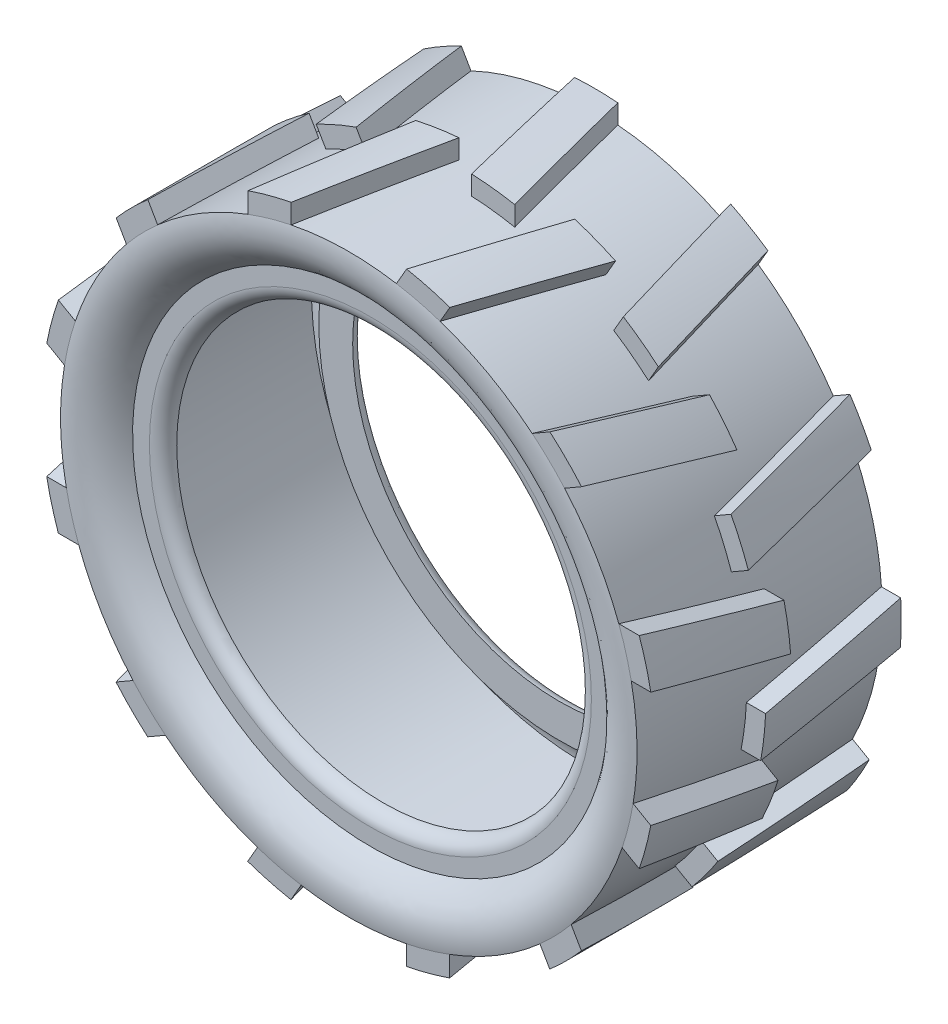
SolidWorks part; units mm, degrees
material "ABS"
ref_plane "Спереди" through (0, 0, 0) normal (0, 0, 1) x (1, 0, 0)
ref_plane "Сверху" through (0, 0, 0) normal (0, 1, 0) x (1, 0, 0)
ref_plane "Справа" through (0, 0, 0) normal (1, 0, 0) x (0, 0, -1)
sketch "Эскиз1" plane through (0, 0, 0) normal (1, 0, 0) x (0, 0, -1)
  line L0 (-131.0476, 0) -> (127.548, 0) construction
  line L1 (0, 0) -> (0, 104.7617) construction
  line L2 (0, 60) -> (25.5, 60)
  line L3 (21, 49.5) -> (21, 46)
  line L5 (18.3095, 50.0522) -> (18.3095, 46)
  line L14 (18.3095, 46) -> (18.3095, 43)
  line L16 (25.5, 60) -> (21, 49.5) construction
  line L17 (0, 57.3095) -> (21.4198, 57.3095) construction
  line L18 (21.4198, 57.3095) -> (18.3095, 50.0522) construction
  line L20 (19.831, 51.1228) -> (18.3095, 50.0522)
  line L21 (-19.831, 51.1228) -> (-18.3095, 50.0522)
  line L23 (-18.3095, 46) -> (-18.3095, 43)
  line L24 (-18.3095, 50.0522) -> (-18.3095, 46)
  line L25 (-21, 49.5) -> (-21, 46)
  line L26 (0, 60) -> (-25.5, 60)
  line L27 (0, 57) -> (23.7272, 57)
  line L28 (0, 57) -> (-23.7272, 57)
  line L32 (0, 58) -> (23.7544, 58) construction
  arc A0 (21, 46) -> (18.3095, 43) centre (18, 45.984) cw
  arc A1 (-21, 46) -> (-18.3095, 43) centre (-18, 45.984) ccw
  spline S0 degree 2 poles (25.5, 60) (26.8739, 53.7315) (21, 49.5) knots 0 0 0 1 1 1
  spline S1 degree 1 poles (23.7544, 58) (19.831, 51.1228) knots 0 0 1 1 construction
  spline S2 degree 3 poles (23.7544, 58) (23.7671, 57.6775) (23.7509, 57.0178) (23.5531, 55.812) (23.1145, 54.6722) (22.4028, 53.5614) (21.7154, 52.7344) (20.8801, 51.9263) (20.1802, 51.3744) (19.831, 51.1228) knots 0.157276 0.157276 0.157276 0.157276 0.262617 0.367957 0.578638 0.683979 0.789319 0.89466 1 1 1 1 only from (23.7272, 57) to (19.831, 51.1228)
  spline S3 degree 3 poles (-23.7272, 57) (-23.6981, 56.6959) (-23.5494, 55.8023) (-23.1145, 54.6722) (-22.4028, 53.5614) (-21.7154, 52.7344) (-20.8801, 51.9263) (-20.1802, 51.3744) (-19.831, 51.1228) knots 0.26618 0.26618 0.26618 0.26618 0.367957 0.578638 0.683979 0.789319 0.89466 1 1 1 1
  spline S4 degree 2 poles (-25.5, 60) (-26.8739, 53.7315) (-21, 49.5) knots 0 0 0 1 1 1
  point P32 (-23.7544, 57)
  dimension "D8" = 3
  dimension "D9" = 3
  dimension "D10" = 21
  dimension "D1" = 46
  dimension "D2" = 60
  dimension "D3" = 3.5
  dimension "D5" = 25.5
  dimension "D6" = 1.8603
  dimension "D7" = 4.0522
  dimension "D11" = 3
  dimension "D4" = 2
revolve "Повернуть1" add sketch "Эскиз1" angle 360 about L0
ref_plane "Плоскость1" through (0, 65, 0) normal (0, 1, 0) x (1, 0, 0)
sketch "Эскиз2" plane through (0, 65, 0) normal (0, 1, 0) x (1, 0, 0)
  line L0 (0, 31.0851) -> (0, -28.8708) construction
  line L1 (-48.8845, 0) -> (54.335, 0) construction
  line L2 (-5.2599, 2.6858) -> (-12, -25.5)
  line L3 (60, -25.5) -> (-60, -25.5) construction
  line L4 (-12, -25.5) -> (-21, -25.5)
  line L5 (-21, -25.5) -> (-14.2599, 2.6858)
  line L6 (-14.2599, 2.6858) -> (-5.2599, 2.6858)
  line L11 (5, 25.5) -> (-4, 25.5)
  line L12 (11.7401, -2.6858) -> (5, 25.5)
  line L13 (-4, 25.5) -> (2.7401, -2.6858)
  line L14 (2.7401, -2.6858) -> (11.7401, -2.6858)
  dimension "D1" = 9
  dimension "D2" = 21
  dimension "D3" = 5
extrude "Бобышка-Вытянуть1" add sketch "Эскиз2" against normal up to surface (6.7192 mm away)
pattern_circular "Круговой массив1" count 12 over 360 about axis through (0, 0, 0) along (0, 0, 1) of "Бобышка-Вытянуть1"
sketch "Эскиз3" plane through (0, 0, 21) normal (0, 0, 1) x (1, 0, 0)
  circle A1 centre (0, 0) radius 64
  circle A2 centre (0, 0) radius 81.6428
  dimension "D1" = 128
extrude "Вырез-Вытянуть1" cut sketch "Эскиз3" against normal through all both and the other way through all
